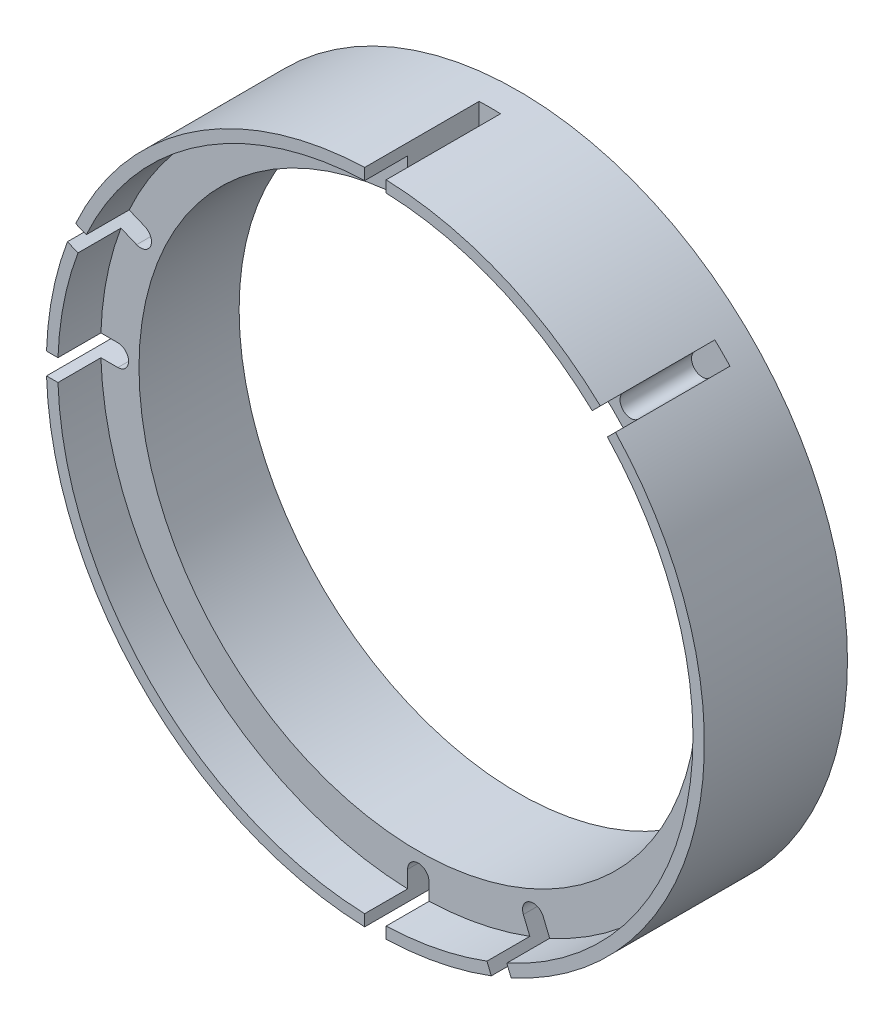
SolidWorks part; units mm, degrees
ref_plane "Front Plane" through (0, 0, 0) normal (0, 0, 1) x (1, 0, 0)
ref_plane "Top Plane" through (0, 0, 0) normal (0, 1, 0) x (1, 0, 0)
ref_plane "Right Plane" through (0, 0, 0) normal (1, 0, 0) x (0, 0, -1)
sketch "Sketch1" plane through (0, 0, 0) normal (0, 0, 1) x (1, 0, 0)
  circle A0 centre (0, 0) radius 23
  dimension "D1" = 46
extrude "Boss-Extrude1" add sketch "Sketch1" along normal mid plane 10
sketch "Sketch2" plane through (0, 0, 5) normal (0, 0, 1) x (1, 0, 0)
  circle A0 centre (0, 0) radius 22.2
  dimension "D1" = 44.4
extrude "Cut-Extrude1" cut sketch "Sketch2" against normal blind 3
sketch "Sketch3" plane through (0, 0, -5) normal (0, 0, -1) x (-1, 0, 0)
  circle A0 centre (0, 0) radius 19.525
  dimension "D1" = 39.05
extrude "Cut-Extrude2" cut sketch "Sketch3" against normal blind 7
sketch "Sketch5" plane through (0, 0, 5) normal (0, 0, 1) x (1, 0, 0)
  line L0 (-23, 0) -> (-21, 0) construction
  line L1 (-23, 0.75) -> (-21, 0.75)
  line L2 (-23, -0.75) -> (-21, -0.75)
  arc A0 (-23, 0.75) -> (-23, -0.75) centre (-23, 0) ccw
  arc A1 (-21, -0.75) -> (-21, 0.75) centre (-21, 0) ccw
  circle A2 centre (0, 0) radius 23 construction
  point P3 (-22, 0)
  point P8 (0, 0)
  dimension "D1" = 21
  dimension "D2" = 1.5
extrude "Cut-Extrude4" cut sketch "Sketch5" against normal blind 8
pattern_circular "CirPattern1" count 16 over 360 about axis through (0, 0, 5) along (0, 0, -1) skipping 1, 2, 3, 6, 7, 8, 9, 11, 13, 14 of "Cut-Extrude4"
